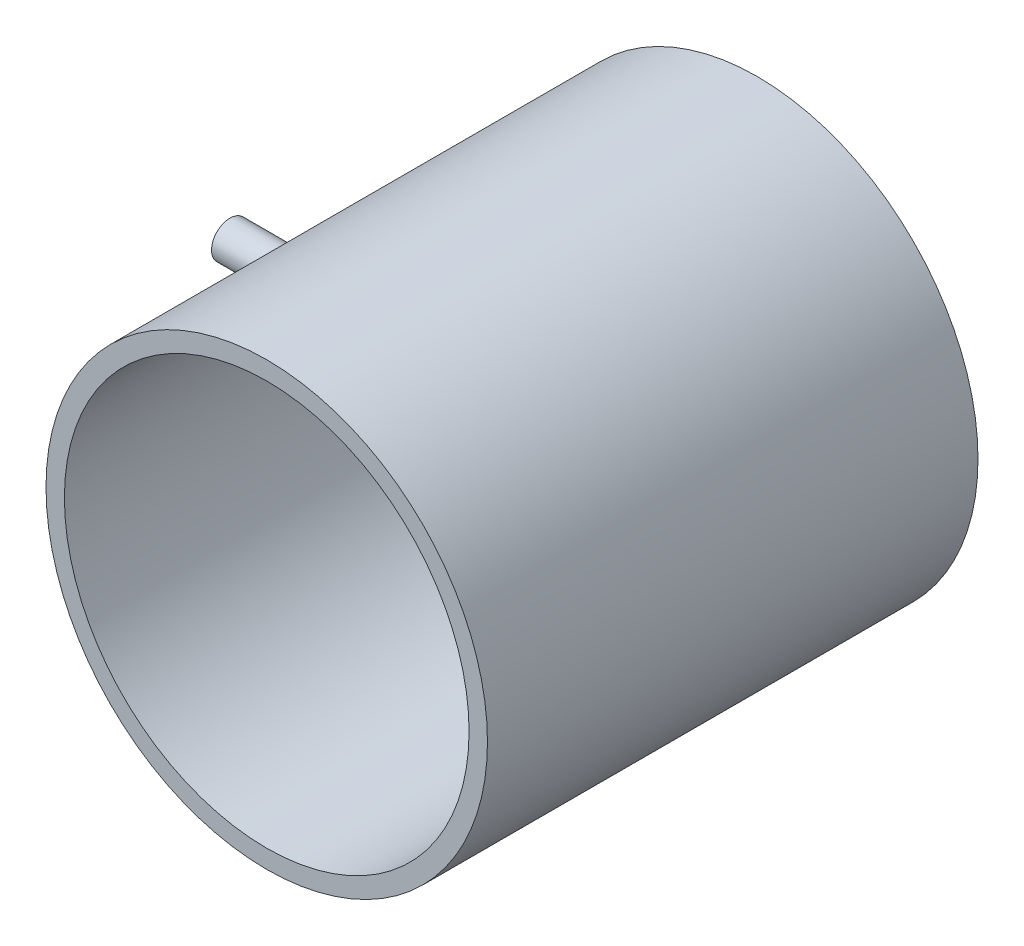
SolidWorks part; units mm, degrees
ref_plane "Plan de face" through (0, 0, 0) normal (0, 0, 1) x (1, 0, 0)
ref_plane "Plan de dessus" through (0, 0, 0) normal (0, 1, 0) x (1, 0, 0)
ref_plane "Plan de droite" through (0, 0, 0) normal (1, 0, 0) x (0, 0, -1)
sketch "Esquisse1" plane through (0, 0, 0) normal (0, 0, 1) x (1, 0, 0)
  line L0 (-37.1413, -0.947) -> (-37.1413, 143.053) construction
  circle A0 centre (-37.1413, 71.053) radius 18
  circle A2 centre (-37.1413, 71.053) radius 16.5
  dimension "D1" = 1.5
  dimension "D2" = 33
extrude "Boss.-Extru.1" add sketch "Esquisse1" against normal blind 40
ref_plane "Plan2" through (-55.1413, 0, 0) normal (-1, 0, 0) x (0, 0, 1)
sketch "Esquisse2" plane through (-55.1413, 0, 0) normal (-1, 0, 0) x (0, 0, 1)
  line L0 (-40, 71.053) -> (0, 71.053) construction
  line L1 (-40, 89.053) -> (-40, 53.053) construction
  line L2 (0, 53.053) -> (0, 89.053) construction
  circle A0 centre (-25, 71.053) radius 1.5
  dimension "D1" = 3
  dimension "D2" = 15
extrude "Boss.-Extru.2" add sketch "Esquisse2" along normal blind 10 and the other way up to surface
